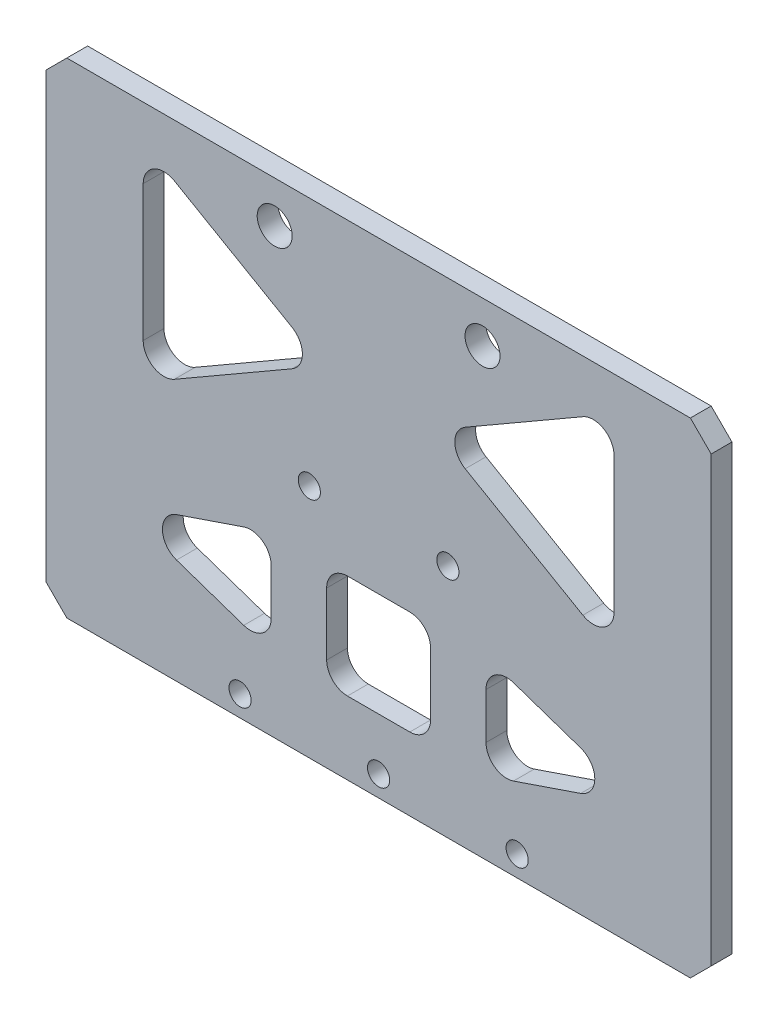
SolidWorks part; units mm, degrees
material "Thornel Mat VMA"
ref_plane "前视基准面" through (0, 0, 0) normal (0, 0, 1) x (1, 0, 0)
ref_plane "上视基准面" through (0, 0, 0) normal (0, 1, 0) x (1, 0, 0)
ref_plane "右视基准面" through (0, 0, 0) normal (1, 0, 0) x (0, 0, -1)
sketch "草图1" plane through (0, 0, 0) normal (1, 0, 0) x (0, 0, -1)
  line L0 (7, 17) -> (7, -17)
  line L1 (10, 20) -> (-10, 20)
  line L2 (10, 20) -> (10, -20)
  line L3 (10, -20) -> (-10, -20)
  line L4 (-10, 20) -> (-10, -20)
  line L5 (10, 20) -> (-10, -20) construction
  line L6 (10, -20) -> (-10, 20) construction
  line L7 (7, -17) -> (-7, -17)
  line L8 (-7, 17) -> (-7, -17)
  line L9 (7, 17) -> (-7, 17)
  point P0 (0, 0)
  dimension "D1" = 40
  dimension "D2" = 20
  dimension "D3" = 3
extrude "凸台-拉伸1" add sketch "草图1" along normal blind 321
sketch "草图2" plane through (0, 20, 0) normal (0, 1, 0) x (1, 0, 0)
  line L0 (160.5, 10) -> (160.5, -10) construction
  line L1 (321, 10) -> (0, 10) construction
  line L2 (321, -10) -> (0, -10) construction
  line L4 (104.5, 5) -> (76.5, 5) construction
  line L5 (104.5, 5) -> (104.5, -5) construction
  line L6 (104.5, -5) -> (76.5, -5) construction
  line L7 (76.5, 5) -> (76.5, -5) construction
  line L8 (104.5, 5) -> (76.5, -5) construction
  line L9 (104.5, -5) -> (76.5, 5) construction
  circle A0 centre (76.5, 5) radius 2.1
  circle A1 centre (76.5, -5) radius 2.1
  circle A2 centre (104.5, -5) radius 2.1
  circle A3 centre (104.5, 5) radius 2.1
  circle A4 centre (216.5, -5) radius 2.1
  circle A5 centre (216.5, 5) radius 2.1
  circle A6 centre (244.5, -5) radius 2.1
  circle A7 centre (244.5, 5) radius 2.1
  point P6 (90.5, 0)
  point P16 (160.5, 0)
  dimension "D3" = 4.2
  dimension "D1" = 140
  dimension "D2" = 10
  dimension "D4" = 28
extrude "切除-拉伸1" [suppressed] cut sketch "草图2" against normal through all
sketch "草图3" [suppressed] plane through (0, -20, 0) normal (0, -1, 0) x (1, 0, 0)
  circle A0 centre (76.5, 5) radius 3.75
  circle A1 centre (76.5, -5) radius 3.75
  circle A2 centre (104.5, 5) radius 3.75
  circle A3 centre (104.5, -5) radius 3.75
  circle A4 centre (216.5, 5) radius 3.75
  circle A5 centre (244.5, 5) radius 3.75
  circle A6 centre (244.5, -5) radius 3.75
  circle A7 centre (216.5, -5) radius 3.75
  dimension "D1" = 7.5
extrude "切除-拉伸2" [suppressed] cut sketch "草图3" against normal up to next
sketch "草图5" plane through (0, 0, 10) normal (0, 0, 1) x (1, 0, 0)
  line L0 (0, -20) -> (10.718, 20)
  line L1 (321, 20) -> (0, 20) construction
  line L2 (10.718, 20) -> (0, 20)
  line L3 (0, 20) -> (0, -20)
  line L4 (321, -20) -> (321, 20)
  line L5 (321, 20) -> (310.282, 20)
  line L6 (310.282, 20) -> (321, -20)
  line L8 (321, -20) -> (0, -20) construction
  dimension "D1" = 75
extrude "切除-拉伸3" [suppressed] cut sketch "草图5" against normal through all
sketch "草图4" [suppressed] plane through (0, 20, 0) normal (0, 1, 0) x (1, 0, 0)
  line L0 (160.5, 10) -> (160.5, -10) construction
  line L1 (310.282, 10) -> (10.718, 10) construction
  line L2 (310.282, -10) -> (10.718, -10) construction
  line L4 (60.718, 4) -> (20.718, 4) construction
  line L5 (60.718, 4) -> (60.718, -4) construction
  line L6 (60.718, -4) -> (20.718, -4) construction
  line L7 (20.718, 4) -> (20.718, -4) construction
  line L8 (60.718, 4) -> (20.718, -4) construction
  line L9 (60.718, -4) -> (20.718, 4) construction
  line L10 (10.718, 10) -> (10.718, -10) construction
  circle A0 centre (20.718, 4) radius 2.1
  circle A1 centre (20.718, -4) radius 2.1
  circle A2 centre (40.718, 4) radius 2.1
  circle A3 centre (40.718, -4) radius 2.1
  circle A4 centre (60.718, 4) radius 2.1
  circle A5 centre (60.718, -4) radius 2.1
  circle A6 centre (300.282, -4) radius 2.1
  circle A7 centre (280.282, -4) radius 2.1
  circle A8 centre (260.282, -4) radius 2.1
  circle A9 centre (260.282, 4) radius 2.1
  circle A10 centre (280.282, 4) radius 2.1
  circle A11 centre (300.282, 4) radius 2.1
  point P6 (40.718, 0)
  point P12 (160.5, 0)
  dimension "D4" = 4.2
  dimension "D1" = 8
  dimension "D2" = 40
  dimension "D3" = 10
extrude "切除-拉伸4" [suppressed] cut sketch "草图4" against normal through all
sketch "草图6" plane through (0, -20, 0) normal (0, -1, 0) x (1, 0, 0)
  line L0 (160.5, 10) -> (160.5, -10) construction
  line L1 (321, 10) -> (0, 10) construction
  line L2 (321, -10) -> (0, -10) construction
  line L4 (180.5, 6) -> (140.5, 6) construction
  line L5 (180.5, 6) -> (180.5, -6) construction
  line L6 (180.5, -6) -> (140.5, -6) construction
  line L7 (140.5, 6) -> (140.5, -6) construction
  line L8 (180.5, 6) -> (140.5, -6) construction
  line L9 (180.5, -6) -> (140.5, 6) construction
  circle A0 centre (140.5, 6) radius 1.6
  circle A1 centre (160.5, 6) radius 1.6
  circle A2 centre (180.5, 6) radius 1.6
  circle A3 centre (180.5, -6) radius 1.6
  circle A4 centre (160.5, -6) radius 1.6
  circle A5 centre (140.5, -6) radius 1.6
  point P6 (160.5, 0)
  dimension "D3" = 3.2
  dimension "D1" = 40
  dimension "D2" = 4
extrude "切除-拉伸5" [suppressed] cut sketch "草图6" against normal up to next
sketch "草图7" plane through (0, 0, 10) normal (0, 0, 1) x (1, 0, 0)
  line L0 (160.5, -20) -> (160.5, 20) construction
  line L1 (321, -20) -> (0, -20) construction
  line L2 (321, 20) -> (0, 20) construction
  line L3 (130.5, -16) -> (150.5, -16) construction
  line L4 (150.5, -16) -> (170.5, -16) construction
  line L5 (140.5, 2) -> (180.5, 2) construction
  line L6 (140.5, 8) -> (180.5, 8)
  line L7 (140.5, -4) -> (180.5, -4)
  circle A0 centre (130.5, -16) radius 1.6 construction
  circle A1 centre (150.5, -16) radius 1.6
  circle A2 centre (170.5, -16) radius 1.6
  circle A3 centre (190.5, -16) radius 1.6 construction
  arc A4 (140.5, 8) -> (140.5, -4) centre (140.5, 2) ccw
  arc A5 (180.5, -4) -> (180.5, 8) centre (180.5, 2) ccw
  point P8 (160.5, -16)
  point P19 (160.5, 2)
  dimension "D1" = 3.2
  dimension "D6" = 6
  dimension "D3" = 20
  dimension "D4" = 4
  dimension "D5" = 40
  dimension "D7" = 18
  dimension "D2" = 4
extrude "切除-拉伸6" [suppressed] cut sketch "草图7" against normal through all both and the other way through all
sketch "草图9" plane through (0, 0, 10) normal (0, 0, 1) x (1, 0, 0)
  line L0 (160.5, 20) -> (160.5, -20) construction
  line L1 (321, 20) -> (0, 20) construction
  line L2 (321, -20) -> (0, -20) construction
  line L3 (55.5, 0) -> (5.5, 0) construction
  line L4 (50.5, 16) -> (10.5, 16) construction
  line L5 (50.5, 16) -> (50.5, -16) construction
  line L6 (50.5, -16) -> (10.5, -16) construction
  line L7 (10.5, 16) -> (10.5, -16) construction
  line L8 (50.5, 16) -> (10.5, -16) construction
  line L9 (50.5, -16) -> (10.5, 16) construction
  line L10 (55.5, -6) -> (5.5, -6)
  line L11 (55.5, 6) -> (5.5, 6)
  line L12 (265.5, 0) -> (315.5, 0) construction
  line L13 (265.5, -6) -> (315.5, -6)
  line L14 (265.5, 6) -> (315.5, 6)
  circle A0 centre (10.5, 16) radius 1.6
  circle A1 centre (30.5, 16) radius 1.6
  circle A2 centre (50.5, 16) radius 1.6
  circle A3 centre (50.5, -16) radius 1.6
  circle A4 centre (30.5, -16) radius 1.6
  circle A5 centre (10.5, -16) radius 1.6
  arc A6 (55.5, -6) -> (55.5, 6) centre (55.5, 0) ccw
  arc A7 (5.5, 6) -> (5.5, -6) centre (5.5, 0) ccw
  arc A8 (265.5, -6) -> (265.5, 6) centre (265.5, 0) cw
  arc A9 (315.5, 6) -> (315.5, -6) centre (315.5, 0) cw
  circle A10 centre (270.5, -16) radius 1.6
  circle A11 centre (290.5, -16) radius 1.6
  circle A12 centre (310.5, -16) radius 1.6
  circle A13 centre (310.5, 16) radius 1.6
  circle A14 centre (290.5, 16) radius 1.6
  circle A15 centre (270.5, 16) radius 1.6
  point P6 (30.5, 0)
  point P12 (160.5, 0)
  point P22 (30.5, 0)
  point P31 (290.5, 0)
  dimension "D4" = 3.2
  dimension "D5" = 6
  dimension "D1" = 4
  dimension "D2" = 40
  dimension "D3" = 110
  dimension "D6" = 50
extrude "切除-拉伸7" [suppressed] cut sketch "草图9" against normal through all
sketch "草图10" plane through (0, 20, 0) normal (0, 1, 0) x (1, 0, 0)
  line L0 (160.5, 10) -> (160.5, -10) construction
  line L1 (40.5, 6) -> (20.5, 6) construction
  line L2 (40.5, 6) -> (40.5, -6) construction
  line L3 (40.5, -6) -> (20.5, -6) construction
  line L4 (20.5, 6) -> (20.5, -6) construction
  line L5 (40.5, 6) -> (20.5, -6) construction
  line L6 (40.5, -6) -> (20.5, 6) construction
  line L7 (321, 10) -> (0, 10) construction
  line L8 (321, -10) -> (0, -10) construction
  circle A0 centre (20.5, 6) radius 1.6
  circle A1 centre (20.5, -6) radius 1.6
  circle A2 centre (40.5, -6) radius 1.6
  circle A3 centre (40.5, 6) radius 1.6
  circle A4 centre (280.5, -6) radius 1.6
  circle A5 centre (280.5, 6) radius 1.6
  circle A6 centre (300.5, -6) radius 1.6
  circle A7 centre (300.5, 6) radius 1.6
  point P0 (30.5, 0)
  point P12 (160.5, 0)
  dimension "D4" = 3.2
  dimension "D1" = 20
  dimension "D2" = 4
  dimension "D3" = 120
extrude "切除-拉伸8" [suppressed] cut sketch "草图10" against normal through all
sketch "草图11" [suppressed] plane through (0, 20, 0) normal (0, 1, 0) x (1, 0, 0)
  line L0 (70.45, 10) -> (70.45, -10)
  line L3 (449.282, 10) -> (10.718, 10) construction
  line L4 (449.282, -10) -> (10.718, -10) construction
  line L5 (10.45, 9) -> (10.45, -9) construction
  dimension "D1" = 60
sketch "草图12" plane through (0, 20, 0) normal (0, 1, 0) x (1, 0, 0)
  line L0 (160.5, 10) -> (160.5, -49990) construction
  line L1 (321, 10) -> (0, 10) construction
  line L2 (0, 0) -> (-50000, 0) construction
  line L3 (0, 10) -> (0, -10) construction
  line L4 (130.5, 0) -> (160.5, 0) construction
  circle A0 centre (130.5, 0) radius 2.6
  circle A1 centre (160.5, 0) radius 2.6
  circle A2 centre (190.5, 0) radius 2.6
  point P4 (160.5, 10)
  point P9 (0, 0)
  dimension "D1" = 5.2
  dimension "D2" = 30
  dimension "D4" = 30
  dimension "D3" = 3
extrude "切除-拉伸9" [suppressed] cut sketch "草图12" against normal up to next
sketch "草图13" [suppressed] plane through (0, 0, 10) normal (0, 0, 1) x (1, 0, 0)
  line L0 (246.6, 20) -> (242.4, 20) construction
  line L1 (246.6, 20) -> (242.4, 20) construction
  line L2 (218.6, 20) -> (214.4, 20) construction
  line L3 (218.6, 20) -> (214.4, 20) construction
  line L4 (214.4, 20) -> (218.6, 20) construction
  line L5 (214.4, 20) -> (214.4, -20) construction
  line L6 (218.6, 20) -> (218.6, -20) construction
  line L7 (214.4, -20) -> (218.6, -20) construction
  line L8 (242.4, 20) -> (246.6, 20) construction
  line L9 (242.4, 20) -> (242.4, -20) construction
  line L10 (246.6, 20) -> (246.6, -20) construction
  line L11 (242.4, -20) -> (246.6, -20) construction
  line L12 (321, -20) -> (0, -20) construction
  line L13 (218.6, 20) -> (242.4, 20) construction
  line L14 (311, 20) -> (311, -49980) construction
  line L15 (321, 0) -> (50321, 0) construction
  line L16 (321, 20) -> (321, -20) construction
  line L17 (311, 13) -> (311, 0) construction
  line L18 (311, 13) -> (287, 13) construction
  line L19 (160.5, 20) -> (160.5, -49980) construction
  line L20 (321, 20) -> (0, 20) construction
  circle A0 centre (311, 13) radius 2.1
  circle A1 centre (311, 0) radius 2.1
  circle A2 centre (311, -13) radius 2.1
  circle A3 centre (287, 13) radius 2.1
  circle A4 centre (287, 0) radius 2.1
  circle A5 centre (287, -13) radius 2.1
  circle A6 centre (10, 13) radius 2.1
  circle A7 centre (10, 0) radius 2.1
  circle A8 centre (10, -13) radius 2.1
  circle A9 centre (34, -13) radius 2.1
  circle A10 centre (34, 0) radius 2.1
  circle A11 centre (34, 13) radius 2.1
  point P17 (321, 0)
  point P38 (160.5, 20)
  dimension "D1" = 4.2
  dimension "D2" = 13
  dimension "D4" = 13
  dimension "D6" = 24
  dimension "D7" = 10
  dimension "D3" = 3
  dimension "D5" = 2
sketch "草图14" plane through (0, 20, 0) normal (0, 1, 0) x (1, 0, 0)
  line L0 (160.5, 10) -> (160.5, -49990) construction
  line L1 (321, 10) -> (0, 10) construction
  line L2 (321, 0) -> (50321, 0) construction
  line L3 (321, 10) -> (321, -10) construction
  line L5 (286.5, 5) -> (314.5, 5) construction
  line L6 (286.5, 5) -> (286.5, -5) construction
  line L7 (286.5, -5) -> (314.5, -5) construction
  line L8 (314.5, 5) -> (314.5, -5) construction
  line L9 (300.5, -5) -> (300.5, 5) construction
  line L10 (286.5, 0) -> (314.5, 0) construction
  circle A0 centre (314.5, 5) radius 2.1
  circle A1 centre (314.5, -5) radius 2.1
  circle A2 centre (286.5, -5) radius 2.1
  circle A3 centre (286.5, 5) radius 2.1
  circle A4 centre (34.5, -5) radius 2.1
  circle A5 centre (6.5, -5) radius 2.1
  circle A6 centre (6.5, 5) radius 2.1
  circle A7 centre (34.5, 5) radius 2.1
  point P4 (160.5, 10)
  point P9 (321, 0)
  point P10 (300.5, 0)
  dimension "D4" = 4.2
  dimension "D1" = 10
  dimension "D2" = 28
  dimension "D3" = 140
extrude "切除-拉伸11" [suppressed] cut sketch "草图14" against normal through all
extrude "切除-拉伸10" [suppressed] cut sketch "草图13" against normal through all
sketch "草图15" plane through (0, 0, 10) normal (0, 0, 1) x (1, 0, 0)
  line L0 (160.5, 20) -> (160.5, -49980) construction
  line L1 (321, 20) -> (0, 20) construction
  circle A0 centre (145.5, 14) radius 2.525
  circle A1 centre (175.5, 14) radius 2.525
  point P4 (160.5, 20)
  dimension "D1" = 5.05
  dimension "D2" = 6
  dimension "D3" = 15
extrude "切除-拉伸12" cut sketch "草图15" against normal through all
sketch "草图18" plane through (321, 0, 0) normal (1, 0, 0) x (0, 0, -1)
  line L0 (-10, -20) -> (10, -20) construction
  line L1 (10, 20) -> (-7, 20)
  line L2 (10, 20) -> (10, -20)
  line L3 (10, -20) -> (-7, -20)
  line L4 (-7, 20) -> (-7, -20)
  line L5 (1.5, -20) -> (1.5, 20) construction
  line L6 (10, 0) -> (-7, 0) construction
  line L7 (-7, 17) -> (-7, -17) construction
  point P316 (1.5, 0)
extrude "切除-拉伸14" cut sketch "草图18" against normal through all
sketch "草图19" plane through (0, 0, 10) normal (0, 0, 1) x (1, 0, 0)
  line L0 (160.5, 20) -> (160.5, -49980) construction
  line L1 (321, 20) -> (0, 20) construction
  line L2 (321, -20) -> (0, -20) construction
  line L3 (112.5, -20) -> (208.5, -20)
  line L4 (112.5, -20) -> (112.5, -50)
  line L5 (112.5, -50) -> (208.5, -50)
  line L6 (208.5, -20) -> (208.5, -50)
  line L7 (160.5, -50) -> (160.5, -20) construction
  line L8 (112.5, -35) -> (208.5, -35) construction
  point P4 (160.5, 20)
  point P149 (160.5, -35)
  dimension "D1" = 96
  dimension "D2" = 30
extrude "凸台-拉伸2" add sketch "草图19" against normal up to surface (3 mm away) up to face at (145.5, 16.525, 7)
sketch "草图17" plane through (0, 0, 10) normal (0, 0, 1) x (1, 0, 0)
  line L0 (160.5, 20) -> (160.5, -49980) construction
  line L1 (321, 20) -> (0, 20) construction
  line L2 (222, -14) -> (-49778, -14) construction
  line L3 (321, -20) -> (208.5, -20) construction
  line L4 (292, 16.5) -> (-49708, 16.5) construction
  line L5 (321, 20) -> (321, -20) construction
  line L6 (112.5, -47) -> (208.5, -47) construction
  line L9 (112.5, -20) -> (112.5, -50) construction
  line L10 (208.5, -50) -> (208.5, -20) construction
  line L11 (112.5, -50) -> (208.5, -50) construction
  line L12 (140.5, -47) -> (160.5, -47) construction
  circle A0 centre (12, 16.5) radius 1.6
  circle A1 centre (29, 16.5) radius 1.6
  circle A2 centre (12, -14) radius 1.6
  circle A3 centre (29, -14) radius 1.6
  circle A4 centre (43.5, -14) radius 1.6
  circle A5 centre (67.5, -14) radius 1.6
  circle A6 centre (222, -14) radius 1.6
  circle A7 centre (239, -14) radius 1.6
  circle A8 centre (253.5, -14) radius 1.6
  circle A9 centre (277.5, -14) radius 1.6
  circle A10 centre (292, -14) radius 1.6
  circle A11 centre (309, -14) radius 1.6
  circle A12 centre (82, -14) radius 1.6
  circle A13 centre (99, -14) radius 1.6
  circle A14 centre (292, 16.5) radius 1.6
  circle A15 centre (309, 16.5) radius 1.6
  circle A16 centre (140.5, -47) radius 1.6
  circle A17 centre (160.5, -47) radius 1.6
  circle A18 centre (180.5, -47) radius 1.6
  point P9 (160.5, 20)
  dimension "D2" = 3.5
  dimension "3" = 3.2
  dimension "D12" = 3.2
  dimension "D1" = 6
  dimension "D3" = 12
  dimension "D4" = 17
  dimension "D5" = 61.5
  dimension "D6" = 17
  dimension "D7" = 14.5
  dimension "D8" = 12
  dimension "D9" = 17
  dimension "D10" = 14.5
  dimension "D11" = 3
  dimension "D14" = 20
  dimension "D13" = 3
extrude "切除-拉伸13" cut sketch "草图17" against normal through all
fillet "圆角1" radius 2 2 edges at (208.5, -20, 8.5) (112.5, -20, 8.5)
chamfer "倒角1" distance 3 angle 45 6 edges at (0, -20, 8.5) (0, 20, 8.5) (321, 20, 8.5) (321, -20, 8.5) (208.5, -50, 8.5) (112.5, -50, 8.5)
sketch "草图20" plane through (0, 0, 10) normal (0, 0, 1) x (1, 0, 0)
  line L0 (160.5, 20) -> (160.5, -49980) construction
  line L1 (318, 20) -> (3, 20) construction
  line L2 (306, -10) -> (295, -10)
  line L3 (15, 12.5) -> (26, 12.5)
  line L4 (12, 16.5) -> (29, 16.5) construction
  line L5 (12, 16.5) -> (12, -14) construction
  line L6 (12, -14) -> (29, -14) construction
  line L7 (29, 16.5) -> (29, -14) construction
  line L8 (20.5, -14) -> (20.5, 16.5) construction
  line L9 (12, 1.25) -> (29, 1.25) construction
  line L10 (15, 12.5) -> (15, -10)
  line L11 (15, -10) -> (26, -10)
  line L12 (26, 12.5) -> (26, -10)
  line L13 (20.5, -10) -> (20.5, 12.5) construction
  line L14 (15, 1.25) -> (26, 1.25) construction
  line L15 (295, 12.5) -> (295, -10)
  line L16 (306, 12.5) -> (295, 12.5)
  line L17 (306, 12.5) -> (306, -10)
  line L18 (115.5, -50) -> (205.5, -50) construction
  line L19 (153, -24.5) -> (168, -24.5)
  line L20 (153, -24.5) -> (153, -39.5)
  line L21 (153, -39.5) -> (168, -39.5)
  line L22 (168, -24.5) -> (168, -39.5)
  line L23 (160.5, -39.5) -> (160.5, -24.5) construction
  line L24 (153, -32) -> (168, -32) construction
  line L25 (123, -32) -> (145, -24.5)
  line L26 (145, -24.5) -> (145, -39.5)
  line L27 (145, -39.5) -> (123, -32)
  line L28 (176, -24.5) -> (176, -39.5)
  line L29 (198, -32) -> (176, -24.5)
  line L30 (176, -39.5) -> (198, -32)
  point P4 (160.5, 20)
  point P5 (20.5, 1.25)
  point P17 (160.5, -32)
  point P238 (20.5, 1.25)
  dimension "D1" = 4
  dimension "D2" = 3
  dimension "D3" = 15
  dimension "D4" = 8
  dimension "15" = 15
  dimension "20" = 18
  dimension "D5" = 30
extrude "切除-拉伸15" cut sketch "草图20" against normal through all
fillet "圆角2" radius 3 18 edges at (306, -10, 8.5) (295, -10, 8.5) (295, 12.5, 8.5) (306, 12.5, 8.5) (168, -39.5, 8.5) (153, -39.5, 8.5) (153, -24.5, 8.5) (168, -24.5, 8.5) (123, -32, 8.5) (145, -24.5, 8.5) (145, -39.5, 8.5) (198, -32, 8.5) (176, -39.5, 8.5) (176, -24.5, 8.5) (26, -10, 8.5) (15, -10, 8.5) (26, 12.5, 8.5) (15, 12.5, 8.5)
sketch "草图21" plane through (0, 0, 10) normal (0, 0, 1) x (1, 0, 0)
  line L0 (160.5, 20) -> (160.5, -49980) construction
  line L1 (318, 20) -> (3, 20) construction
  line L2 (1029, -14) -> (-49971, -14) construction
  line L3 (321, 0) -> (0, 0) construction
  line L4 (321, 17) -> (321, -17) construction
  line L5 (29, 14) -> (29, -14) construction
  line L6 (29, -14) -> (67.5, 14) construction
  line L7 (67.5, 14) -> (99, -14) construction
  line L8 (99, -14) -> (129.5, 14) construction
  line L9 (129.5, 14) -> (160.5, -14) construction
  line L10 (160.5, -14) -> (191.5, 14) construction
  line L11 (191.5, 14) -> (222, -14) construction
  line L12 (222, -14) -> (253.5, 14) construction
  line L13 (253.5, 14) -> (292, -14) construction
  line L14 (292, -14) -> (292, 14) construction
  line L15 (292, 14) -> (253.5, -14) construction
  line L16 (253.5, -14) -> (222, 14) construction
  line L17 (222, 14) -> (191.5, -14) construction
  line L18 (191.5, -14) -> (160.5, 14) construction
  line L19 (160.5, 14) -> (129.5, -14) construction
  line L20 (129.5, -14) -> (99, 14) construction
  line L21 (99, 14) -> (67.5, -14) construction
  line L22 (67.5, -14) -> (29, 14) construction
  line L23 (29, 14) -> (292, 14) construction
  line L24 (98.9568, 8.6097) -> (70.1575, -16.9896) construction
  line L25 (33, 6.1449) -> (33, -10)
  line L26 (181.1038, -10) -> (139.8962, -10)
  line L27 (67.2489, -8.8714) -> (41.3007, 10)
  line L28 (160.5, 8.6099) -> (132.1811, -16.9684) construction
  line L29 (98.9568, 8.6097) -> (78.0208, -10) construction
  line L30 (150.1038, 10) -> (129.5219, -8.5901) construction
  line L31 (129.5219, -8.5901) -> (109.2719, 10) construction
  line L32 (157.8189, 16.9684) -> (129.5219, -8.5901) construction
  line L33 (160.5, 8.6099) -> (139.8962, -10)
  line L34 (253.7511, -8.8714) -> (224.6575, 16.9896) construction
  line L35 (191.4781, -8.5901) -> (170.8962, 10) construction
  line L36 (288, -10) -> (265.8007, -10)
  line L37 (222.0432, 8.6097) -> (201.7719, -10) construction
  line L38 (288, -14) -> (288, 6.1449) construction
  line L39 (253.7511, -8.8714) -> (232.5208, 10)
  line L40 (288, -10) -> (288, 6.1449)
  line L41 (288, 6.1449) -> (265.8007, -10)
  line L43 (41.3007, 10) -> (88.4792, 10)
  line L45 (33, 6.1449) -> (33, -14) construction
  line L46 (29, 10) -> (292, 10) construction
  line L47 (55.1993, -10) -> (33, -10)
  line L48 (67.2489, -8.8714) -> (31.3527, 17.2349) construction
  line L49 (55.1993, -10) -> (33, 6.1449)
  line L50 (65.1473, -17.2349) -> (33, 6.1449) construction
  line L51 (88.4792, 10) -> (67.2489, -8.8714)
  line L52 (96.3425, 16.9896) -> (67.2489, -8.8714) construction
  line L53 (109.2719, 10) -> (150.1038, 10) construction
  line L54 (119.2281, -10) -> (78.0208, -10) construction
  line L55 (119.2281, -10) -> (98.9568, 8.6097) construction
  line L56 (126.7949, -16.9466) -> (98.9568, 8.6097) construction
  line L57 (181.1038, -10) -> (160.5, 8.6099)
  line L58 (129.5219, -8.5901) -> (101.7051, 16.9466) construction
  line L59 (188.8189, -16.9684) -> (160.5, 8.6099) construction
  line L60 (222.0432, 8.6097) -> (194.2051, -16.9466) construction
  line L61 (211.7281, 10) -> (191.4781, -8.5901) construction
  line L62 (191.4781, -8.5901) -> (163.1811, 16.9684) construction
  line L63 (170.8962, 10) -> (211.7281, 10) construction
  line L64 (219.2949, 16.9466) -> (191.4781, -8.5901) construction
  line L65 (242.9792, -10) -> (201.7719, -10) construction
  line L66 (232.5208, 10) -> (279.6993, 10)
  line L67 (242.9792, -10) -> (222.0432, 8.6097) construction
  line L68 (250.8425, -16.9896) -> (222.0432, 8.6097) construction
  line L69 (288, 6.1449) -> (255.8527, -17.2349) construction
  line L70 (279.6993, 10) -> (253.7511, -8.8714)
  line L71 (289.6473, 17.2349) -> (253.7511, -8.8714) construction
  circle A0 centre (29, -14) radius 1.6 construction
  circle A1 centre (29, -14) radius 1.6 construction
  circle A2 centre (67.5, -14) radius 1.6 construction
  circle A3 centre (67.5, -14) radius 1.6 construction
  circle A4 centre (99, -14) radius 1.6 construction
  circle A5 centre (99, -14) radius 1.6 construction
  circle A6 centre (222, -14) radius 1.6 construction
  arc A7 (251.9, -14) -> (255.1, -14) centre (253.5, -14) cw construction
  circle A8 centre (292, -14) radius 1.6 construction
  circle A9 centre (160.5, -14) radius 1.6 construction
  circle A10 centre (129.5, -14) radius 1.6 construction
  circle A11 centre (191.5, -14) radius 1.6 construction
  circle A12 centre (129.5, 14) radius 1.6 construction
  circle A13 centre (160.5, 14) radius 1.6 construction
  circle A14 centre (292, 14) radius 1.6 construction
  circle A15 centre (253.5, 14) radius 1.6 construction
  circle A16 centre (222, 14) radius 1.6 construction
  circle A17 centre (99, 14) radius 1.6 construction
  circle A18 centre (67.5, 14) radius 1.6 construction
  circle A19 centre (29, 14) radius 1.6 construction
  circle A20 centre (191.5, 14) radius 1.6 construction
  point P13 (160.5, 20)
  dimension "D1" = 31
  dimension "D11" = 4
  dimension "D13" = 4
  dimension "D2" = 4
  dimension "D3" = 4
  dimension "D4" = 4
  dimension "D5" = 4
  dimension "D6" = 4
  dimension "D7" = 4
  dimension "D8" = 4
  dimension "D9" = 4
  dimension "D10" = 4
  dimension "D12" = 4
extrude "切除-拉伸16" cut sketch "草图21" against normal through all
fillet "圆角3" radius 2 15 edges at (55.1993, -10, 8.5) (33, -10, 8.5) (288, 6.1449, 8.5) (288, -10, 8.5) (265.8007, -10, 8.5) (253.7511, -8.8714, 8.5) (232.5208, 10, 8.5) (279.6993, 10, 8.5) (67.2489, -8.8714, 8.5) (41.3007, 10, 8.5) (88.4792, 10, 8.5) (181.1038, -10, 8.5) (139.8962, -10, 8.5) (160.5, 8.6099, 8.5) (33, 6.1449, 8.5)
sketch "草图22" plane through (0, 0, 10) normal (0, 0, 1) x (1, 0, 0)
  line L0 (115.5, -50) -> (205.5, -50) construction
  line L1 (160.5, -50) -> (160.5, 26.6674) construction
  circle A2 centre (150.5, -16) radius 1.6
  circle A3 centre (170.5, -16) radius 1.6
  dimension "D1" = 3.2
  dimension "D2" = 34
  dimension "D3" = 10
extrude "切除-拉伸17" cut sketch "草图22" against normal through all
sketch "草图26" plane through (0, 0, 10) normal (0, 0, 1) x (1, 0, 0)
  line L0 (112.5, -22) -> (112.5, 20)
  line L1 (208.5, -22) -> (208.5, 20)
  line L2 (112.5, 20) -> (-3, 20)
  line L14 (0, 17) -> (0, -17)
  line L16 (3, -20) -> (110.5, -20)
  line L17 (112.5, -22) -> (112.5, -47)
  line L19 (115.5, -50) -> (205.5, -50)
  line L21 (208.5, -47) -> (208.5, -22)
  line L22 (210.5, -20) -> (318, -20)
  line L23 (0, -17) -> (3, -20)
  line L24 (321, -17) -> (321, 17)
  line L25 (0, -17) -> (3, -20)
  line L26 (318, 20) -> (3, 20)
  line L27 (112.5, -47) -> (115.5, -50)
  line L28 (0, 17) -> (0, -17)
  line L30 (3, -20) -> (110.5, -20)
  line L36 (210.5, -20) -> (318, -20)
  line L38 (321, -17) -> (321, 17)
  line L40 (318, 20) -> (208.5, 20)
  line L41 (205.5, -50) -> (208.5, -47)
  line L42 (318, -20) -> (321, -17)
  line L43 (318, -20) -> (321, -17)
  line L44 (321, 17) -> (318, 20)
  line L45 (321, 17) -> (318, 20)
  line L46 (3, 20) -> (0, 17)
  line L47 (3, 20) -> (0, 17)
  arc A2 (112.5, -22) -> (110.5, -20) centre (110.5, -22) ccw
  arc A3 (210.5, -20) -> (208.5, -22) centre (210.5, -22) ccw
  arc A4 (112.5, -22) -> (110.5, -20) centre (110.5, -22) ccw
  arc A5 (210.5, -20) -> (208.5, -22) centre (210.5, -22) ccw
  dimension "D1" = 0
extrude "切除-拉伸19" cut sketch "草图26" against normal blind 10 contours A4 L0 L2 L47 L28 L25 L30 | A5 L36 L43 L38 L45 L40 L1
chamfer "倒角2" distance 3 angle 45 2 edges at (208.5, 20, 8.5) (112.5, 20, 8.5)
sketch "草图27" plane through (0, 0, 10) normal (0, 0, 1) x (1, 0, 0)
  line L0 (145.0943, -10) -> (175.9057, -10) construction
  line L1 (177.2463, -6.5158) -> (161.8406, 7.3991) construction
  line L2 (159.1594, 7.3991) -> (143.7537, -6.5158) construction
  line L3 (145.0943, -10) -> (175.9057, -10)
  line L4 (177.2463, -6.5158) -> (161.8406, 7.3991)
  line L5 (159.1594, 7.3991) -> (143.7537, -6.5158)
  arc A0 (175.9057, -10) -> (177.2463, -6.5158) centre (175.9057, -8) ccw construction
  arc A1 (143.7537, -6.5158) -> (145.0943, -10) centre (145.0943, -8) ccw construction
  arc A2 (161.8406, 7.3991) -> (159.1594, 7.3991) centre (160.5, 5.9149) ccw construction
  arc A3 (175.9057, -10) -> (177.2463, -6.5158) centre (175.9057, -8) ccw
  arc A4 (143.7537, -6.5158) -> (145.0943, -10) centre (145.0943, -8) ccw
  arc A5 (161.8406, 7.3991) -> (159.1594, 7.3991) centre (160.5, 5.9149) ccw
extrude "凸台-拉伸3" add sketch "草图27" against normal up to surface (3 mm away) up to face at (160.5, -15, 7)
sketch "草图28" plane through (0, 0, 10) normal (0, 0, 1) x (1, 0, 0)
  line L0 (126.5192, 15) -> (152.5, 0)
  line L1 (205.5, 20) -> (115.5, 20) construction
  line L2 (152.5, 0) -> (126.5192, -15)
  line L3 (126.5192, -15) -> (126.5192, 15)
  line L4 (160.5, 20) -> (160.5, -49980) construction
  line L5 (112.5, 0) -> (208.5, 0) construction
  line L6 (112.5, 17) -> (112.5, -47) construction
  line L7 (208.5, -47) -> (208.5, 17) construction
  line L8 (168.5, 0) -> (194.4808, -15)
  line L9 (194.4808, 15) -> (168.5, 0)
  line L10 (194.4808, -15) -> (194.4808, 15)
  point P4 (160.5, 20)
  dimension "D1" = 30
  dimension "D2" = 8
  dimension "15" = 20
extrude "切除-拉伸20" cut sketch "草图28" against normal through all
fillet "圆角4" radius 3 6 edges at (194.4808, 15, 8.5) (194.4808, -15, 8.5) (168.5, 0, 8.5) (152.5, 0, 8.5) (126.5192, -15, 8.5) (126.5192, 15, 8.5)
